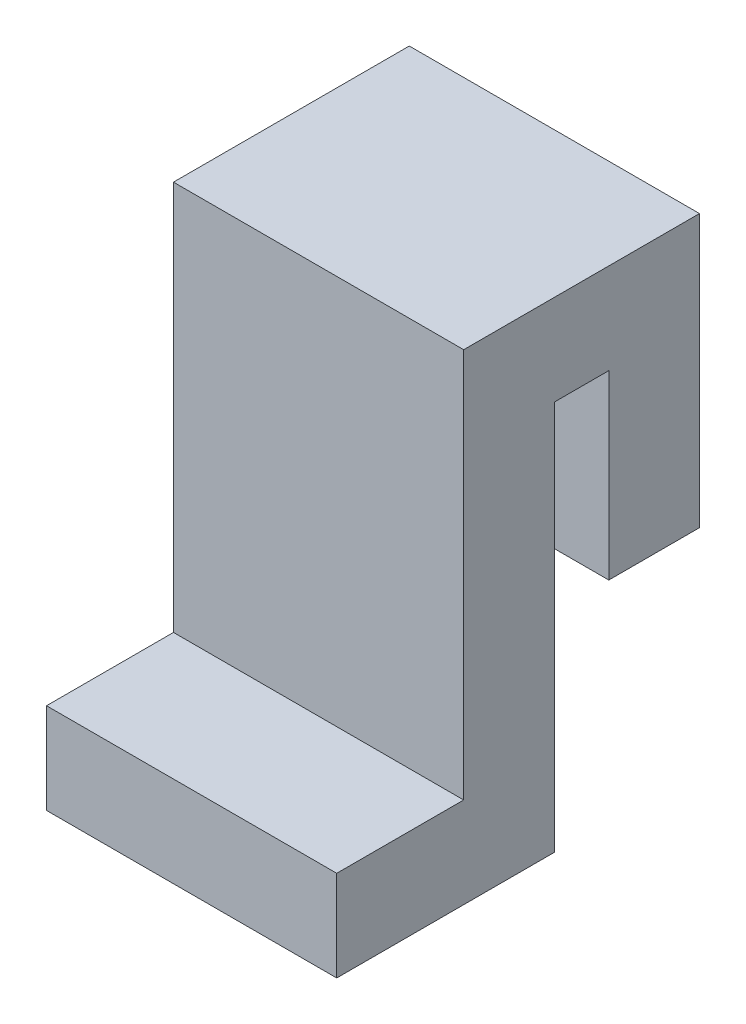
SolidWorks part; units mm, degrees
ref_plane "Front Plane" through (0, 0, 0) normal (0, 0, 1) x (1, 0, 0)
ref_plane "Top Plane" through (0, 0, 0) normal (0, 1, 0) x (1, 0, 0)
ref_plane "Right Plane" through (0, 0, 0) normal (1, 0, 0) x (0, 0, -1)
sketch "Sketch1" plane through (0, 0, 0) normal (1, 0, 0) x (0, 0, -1)
  line L0 (-63.5, 273.05) -> (63.5, -273.05) construction
  line L1 (-241.3, -273.05) -> (-63.5, -273.05)
  line L2 (-241.3, -273.05) -> (-241.3, -400.05)
  line L3 (-241.3, -400.05) -> (63.5, -400.05)
  line L4 (63.5, -273.05) -> (63.5, -400.05)
  line L5 (63.5, 273.05) -> (63.5, 146.05) construction
  line L6 (63.5, -273.05) -> (63.5, 146.05)
  line L7 (63.5, 273.05) -> (-63.5, 273.05)
  line L8 (-63.5, -273.05) -> (-63.5, 273.05)
  line L9 (63.5, 273.05) -> (266.7, 273.05)
  line L10 (-63.5, -273.05) -> (63.5, -273.05) construction
  line L11 (63.5, 146.05) -> (139.7, 146.05)
  line L12 (266.7, 273.05) -> (266.7, 146.05)
  line L13 (139.7, 146.05) -> (266.7, 146.05) construction
  line L14 (266.7, 146.05) -> (266.7, -107.95)
  line L15 (266.7, -107.95) -> (139.7, -107.95)
  line L16 (139.7, 146.05) -> (139.7, -107.95)
  dimension "D1" = 304.8
  dimension "D2" = 127
  dimension "D3" = 546.1
  dimension "D4" = 127
  dimension "D5" = 203.2
  dimension "D6" = 127
  dimension "D7" = 254
  dimension "D8" = 127
extrude "Boss-Extrude1" add sketch "Sketch1" along normal mid plane 406.4
